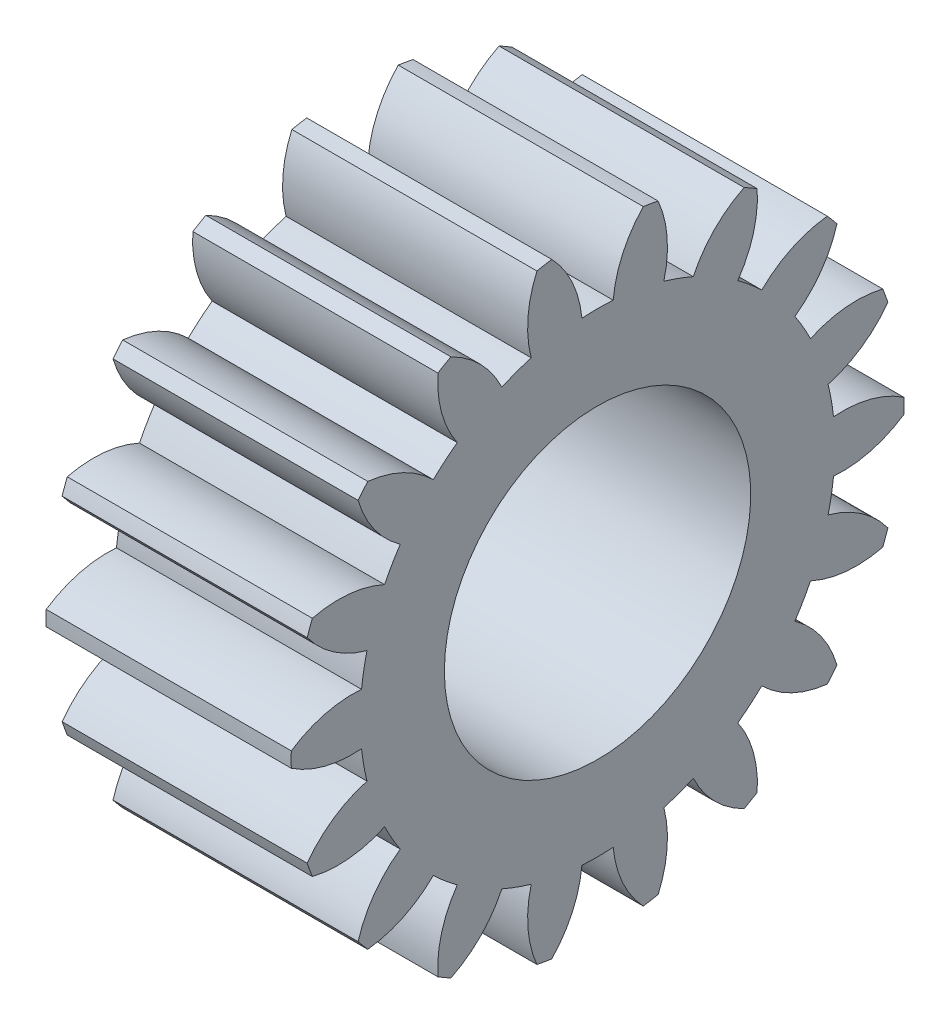
SolidWorks part; units mm, degrees
ref_plane "Plane1" through (0, 0, 0) normal (0, 0, 1) x (1, 0, 0)
ref_plane "Plane2" through (0, 0, 0) normal (0, 1, 0) x (1, 0, 0)
ref_plane "Plane3" through (0, 0, 0) normal (1, 0, 0) x (0, 0, -1)
sketch "HoldingSke" plane through (0, 0, 0) normal (0, 1, 0) x (1, 0, 0)
  line L0 (0, 0) -> (0.9511, -0.309)
  line L1 (-15, 0) -> (100, 0) construction
  line L2 (0, 0) -> (-2.1039, 2.3779)
  line L3 (0, 0) -> (-11.863, 4.5341)
  line L4 (0, 0) -> (8.2133, 2.6687)
  line L5 (0, 0) -> (-46.8476, -17.4728)
  line L6 (0, 0) -> (-6.6317, -4.4744)
  line L7 (-2.1039, 2.3779) -> (8.6586, 51.2059)
  line L8 (-76.2, 54.61) -> (-74.4, 54.61)
  line L9 (-71.009, 38.7566) -> (-53.1078, 45.2721)
  line L10 (-76.2, 71.12) -> (104.1128, 71.12)
  line L11 (0, 0) -> (-8, 0)
  line L12 (-76.2, 101.6) -> (-76.162, 101.6)
  line L13 (24.9733, 27.94) -> (52.9518, 28.4284)
  line L14 (24.9733, 27.94) -> (24.9743, 27.94)
  line L15 (24.9733, 27.94) -> (100.4006, 29.5858)
  line L16 (-63.627, -1) -> (-12.827, -1)
  circle A0 centre (0, 0) radius 5
  circle A1 centre (0, 0) radius 7.749
  circle A2 centre (0, 0) radius 37.5
  circle A3 centre (0, 0) radius 5
  dimension "MHD" = 15.498
  dimension "Hub_dia" = 75
  dimension "Bore" = 10
  dimension "MBD" = 10
  dimension "Num_teeth" = 18
  dimension "Pitch" = 1
  dimension "Overall_len" = 50
  dimension "Show_teeth" = 18
  dimension "Thickness" = 8
  dimension "OAL" = 50.0001
  dimension "T_dim" = 1.8
  dimension "Ap" = 20
  dimension "H" = 19.05
  dimension "Pitch_radius" = 180.3128
  dimension "Width" = 8
  dimension "Backlash" = 0.038
  dimension "Addendum_fac" = 1
  dimension "Dedendum_fac" = 1.25
  dimension "Clearance_fac" = 0.25
  dimension "Dedendum_add" = 0.001
  dimension "Module" = 1
sketch "BasProSke" plane through (0, 0, 0) normal (0, 1, 0) x (1, 0, 0)
  line L0 (-10, 0) -> (60, 0) construction
  line L1 (0, 0) -> (0, 10)
  line L2 (0, 0) -> (8, 0)
  line L3 (8, 0) -> (8, 10)
  line L4 (8, 10) -> (0, 10)
  dimension "Thickness" = 8
  dimension "Diameter" = 20
revolve "Base-Revolve" add sketch "BasProSke" angle 360 about L0
sketch "TooCutSke" plane through (0, 0, 0) normal (1, 0, 0) x (0, 0, -1)
  line L1 (0, 0) -> (0, 107) construction
  line L2 (0, 0) -> (-0.8509, 8.9597) construction
  line L3 (0, 0) -> (-3.1157, 17.6701) construction
  line L4 (-0.8509, 8.9597) -> (-1.5579, 8.835) construction
  arc A0 (0.5106, 7.7322) -> (-0.5106, 7.7322) centre (0, 0) ccw
  arc A1 (1.5152, 9.9102) -> (-1.5152, 9.9102) centre (0, 0) ccw
  circle A2 centre (0, 0) radius 9 construction
  circle A3 centre (0, 0) radius 8.4572 construction
  arc A4 (-0.5106, 7.7322) -> (-1.5152, 9.9102) centre (-4.0952, 7.3996) ccw
  arc A5 (1.5152, 9.9102) -> (0.5106, 7.7322) centre (4.0952, 7.3996) ccw
  dimension "Root_dia" = 15.498
  dimension "Overcut_dia" = 20.0508
  dimension "Pitch_dia" = 18
  dimension "Base_dia" = 16.9145
  dimension "Flank_rad" = 3.6
  dimension "Half_ang" = 10
  dimension "Half_CT" = 0.7179
extrude "ToothCut" cut sketch "TooCutSke" along normal through all
fillet "Breaks" [suppressed] radius 0.02
fillet "RootFillets" [suppressed] radius 0.251
pattern_circular "TeethCuts" count 18 every 20 about axis through (-10, 0, 0) along (1, 0, 0) of "ToothCut", "RootFillets", "Breaks"
sketch "HubNeaOneSke" plane through (0, 0, 0) normal (-1, 0, 0) x (0, 0, 1)
  circle A0 centre (0, 0) radius 7.749
  dimension "Diameter" = 15.498
extrude "HubNearOne" [suppressed] add sketch "HubNeaOneSke" along normal blind 42.0001
sketch "HubNeaBotSke" plane through (0, 0, 0) normal (-1, 0, 0) x (0, 0, 1)
  circle A0 centre (0, 0) radius 7.749
  dimension "Diameter" = 15.498
extrude "HubNearBoth" [suppressed] add sketch "HubNeaBotSke" along normal blind 21
ref_plane "FarPln" through (8, 0, 0) normal (1, 0, 0) x (0, 0, -1)
sketch "HubFarSke" plane through (8, 0, 0) normal (1, 0, 0) x (0, 0, -1)
  circle A0 centre (0, 0) radius 7.749
  dimension "Diameter" = 15.498
extrude "HubFar" [suppressed] add sketch "HubFarSke" along normal blind 21
sketch "BorSke" plane through (0, 0, 0) normal (1, 0, 0) x (0, 0, -1)
  circle A0 centre (0, 0) radius 5
  dimension "Diameter" = 10
extrude "Bore" cut sketch "BorSke" along normal mid plane 100.0001
sketch "KeySke" plane through (0, 0, 0) normal (1, 0, 0) x (0, 0, -1)
  line L0 (-2, 0) -> (-2, 6.8)
  line L1 (-2, 6.8) -> (2, 6.8)
  line L2 (2, 6.8) -> (2, 0)
  line L3 (0, 0) -> (0, 34) construction
  line L4 (-2, 0) -> (2, 0)
  dimension "Offset" = 6.8
  dimension "Width" = 4
extrude "Keyway" [suppressed] cut sketch "KeySke" along normal mid plane 100.0001
pattern_circular "Keyway2" [suppressed] count 2 every 90 about axis through (-10, 0, 0) along (1, 0, 0)
ref_plane "基准面1" through (4, 0, 0) normal (1, 0, 0) x (0, 0, -1)
sketch "草图1" plane through (4, 0, 0) normal (1, 0, 0) x (0, 0, -1)
  line L0 (0, 0) -> (1.7365, 9.8481)
  line L1 (0, 0) -> (6.7108, -3.8745)
ref_plane "基准面2" through (0, 0, 0) normal (0, -0.1736, -0.9848) x (-1, 0, 0)
ref_plane "基准面3" through (0, 0, 0) normal (0, -0.866, 0.5) x (-1, 0, 0)
equation "' \"Module@HoldingSke\" = 6.35"
equation "' \"Num_teeth@HoldingSke\" = 12"
equation "' \"Ap@HoldingSke\" =  20"
equation "' \"Ap@HoldingSke\" = 20"
equation "' \"Width@HoldingSke\" = 0.5 * 25.4"
equation "' \"Hub_dia@HoldingSke\"= 1 * 25.4"
equation "' \"Hub_dia@HoldingSke\" = 1 * 25.4"
equation "' \"Overall_len@HoldingSke\" = 1.0 * 25.4"
equation "' \"Bore@HoldingSke\" = 0.75 * 25.4"
equation "' \"T_dim@HoldingSke\" = 0.1 * 25.4"
equation "' \"Width@KeySke\" = 0.25 * 25.4"
equation "' \"Show_teeth@HoldingSke\" = 13"
equation "' \"Backlash@HoldingSke\" = 0.009 * 25.4"
equation "' \"Addendum_fac@HoldingSke\" = 1.0"
equation "' \"Dedendum_fac@HoldingSke\" = 1.25"
equation "' \"Dedendum_add@HoldingSke\" = 0.00005 * 25.4"
equation "' \"Clearance_fac@HoldingSke\" = 0.25"
equation "\"Pitch@HoldingSke\" = 1 / \"Module@HoldingSke\""
equation "\"Overcut_dia@TooCutSke\" = (\"Num_teeth@HoldingSke\" + 2 * \"Addendum_fac@HoldingSke\") / \"Pitch@HoldingSke\" + 0.002 * 25.4"
equation "\"Pitch_dia@TooCutSke\" = \"Num_teeth@HoldingSke\" / \"Pitch@HoldingSke\""
equation "\"Base_dia@TooCutSke\" = \"Num_teeth@HoldingSke\" / \"Pitch@HoldingSke\" * cos((\"Ap@HoldingSke\"  * 3.14159265 / 180))"
equation "\"Root_dia@TooCutSke\" = (\"Num_teeth@HoldingSke\" + 2) / \"Pitch@HoldingSke\" - 2 * (\"Addendum_fac@HoldingSke\" + \"Dedendum_fac@HoldingSke\") / \"Pitch@HoldingSke\" - \"Dedendum_add@HoldingSke\" * 2"
equation "\"Half_ang@TooCutSke\" = 180 / \"Num_teeth@HoldingSke\""
equation "\"Half_CT@TooCutSke\" = \"Num_teeth@HoldingSke\" / \"Pitch@HoldingSke\" * sin((3.14159265 / 2 / \"Num_teeth@HoldingSke\")) / 2 - 7 * \"Backlash@HoldingSke\" / 4"
equation "\"Flank_rad@TooCutSke\" = \"Num_teeth@HoldingSke\" / \"Pitch@HoldingSke\" / 5"
equation "\"Radius@RootFillets\" = \"Clearance_fac@HoldingSke\" / \"Pitch@HoldingSke\" + \"Dedendum_add@HoldingSke\""
equation "\"Break_rad@Breaks\" = 0.02 / \"Pitch@HoldingSke\""
equation "\"Thickness@HoldingSke\" = \"Width@HoldingSke\""
equation "\"OAL@HoldingSke\" = \"Thickness@HoldingSke\""
equation "\"MHD@HoldingSke\" = (\"Num_teeth@HoldingSke\" + 2) / \"Pitch@HoldingSke\" - 2 * (\"Addendum_fac@HoldingSke\" + \"Dedendum_fac@HoldingSke\")  / \"Pitch@HoldingSke\" - \"Dedendum_add@HoldingSke\" * 2"
equation "\"MBD@HoldingSke\" = (\"Num_teeth@HoldingSke\" + 2) / \"Pitch@HoldingSke\" - 2 * (\"Addendum_fac@HoldingSke\" + \"Dedendum_fac@HoldingSke\")  / \"Pitch@HoldingSke\" - \"Dedendum_add@HoldingSke\" * 2 - 0.002 * 25.4"
equation "\"MHD@HoldingSke\" = ((sgn( \"MHD@HoldingSke\" - \"Hub_dia@HoldingSke\" )-1)*( \"MHD@HoldingSke\" - \"Hub_dia@HoldingSke\" ))/-2+ \"Hub_dia@HoldingSke\""
equation "\"MBD@HoldingSke\" = ((sgn( \"MBD@HoldingSke\" - \"Bore@HoldingSke\" )-1)*( \"MBD@HoldingSke\" - \"Bore@HoldingSke\" ))/-2+ \"Bore@HoldingSke\""
equation "\"OAL@HoldingSke\" = ((sgn( \"OAL@HoldingSke\" - \"Overall_len@HoldingSke\" )+1)*( \"OAL@HoldingSke\" - \"Overall_len@HoldingSke\" ))/2 + \"Overall_len@HoldingSke\" + 0.000002 * 25.4"
equation "\"Num_teeth@TeethCuts\" = int( \"Show_teeth@HoldingSke\" ) + 1"
equation "\"Num_teeth@TeethCuts\" = ((sgn( \"Num_teeth@TeethCuts\" - \"Num_teeth@HoldingSke\" )-1)*( \"Num_teeth@TeethCuts\" - \"Num_teeth@HoldingSke\" ))/-2+ \"Num_teeth@HoldingSke\""
equation "\"Num_teeth@TeethCuts\" = ((sgn( \"Num_teeth@TeethCuts\" - 2.0)+1)*( \"Num_teeth@TeethCuts\" - 2.0))/2 +2.0"
equation "\"Angle@TeethCuts\" = 360.0 / \"Num_teeth@HoldingSke\""
equation "\"Diameter@BasProSke\" = (\"Num_teeth@HoldingSke\" + 2 * \"Addendum_fac@HoldingSke\") / \"Pitch@HoldingSke\""
equation "\"Thickness@BasProSke\"  = \"Thickness@HoldingSke\""
equation "' \"Fillet_rad@BasProSke\" =  \"Thickness@HoldingSke\" * 0.05"
equation "' \"Fillet_rad@BasProSke\" = \"Thickness@HoldingSke\" * 0.05"
equation "\"MHD@HoldingSke\" = ((sgn( \"MHD@HoldingSke\" - \"Root_dia@TooCutSke\" )-1)*( \"MHD@HoldingSke\" - \"Root_dia@TooCutSke\" ))/-2+ \"Root_dia@TooCutSke\""
equation "\"Diameter@HubNeaOneSke\" = \"MHD@HoldingSke\""
equation "\"Length@HubNearOne\" = \"OAL@HoldingSke\" - \"Thickness@BasProSke\""
equation "\"Diameter@HubNeaBotSke\" = \"MHD@HoldingSke\""
equation "\"Length@HubNearBoth\" = ( \"OAL@HoldingSke\" - \"Thickness@BasProSke\" ) / 2.0"
equation "\"Thickness@FarPln\" = \"Thickness@BasProSke\""
equation "\"Diameter@HubFarSke\" = \"MHD@HoldingSke\""
equation "\"Length@HubFar\" = ( \"OAL@HoldingSke\" - \"Thickness@BasProSke\" ) / 2.0"
equation "\"Diameter@BorSke\" = \"MBD@HoldingSke\""
equation "\"D1@Bore\" = \"OAL@HoldingSke\" * 2.0"
equation "\"D1@Keyway\" = \"OAL@HoldingSke\" * 2.0"
equation "\"Offset@KeySke\" = \"T_dim@HoldingSke\" + \"MBD@HoldingSke\" / 2.0"
